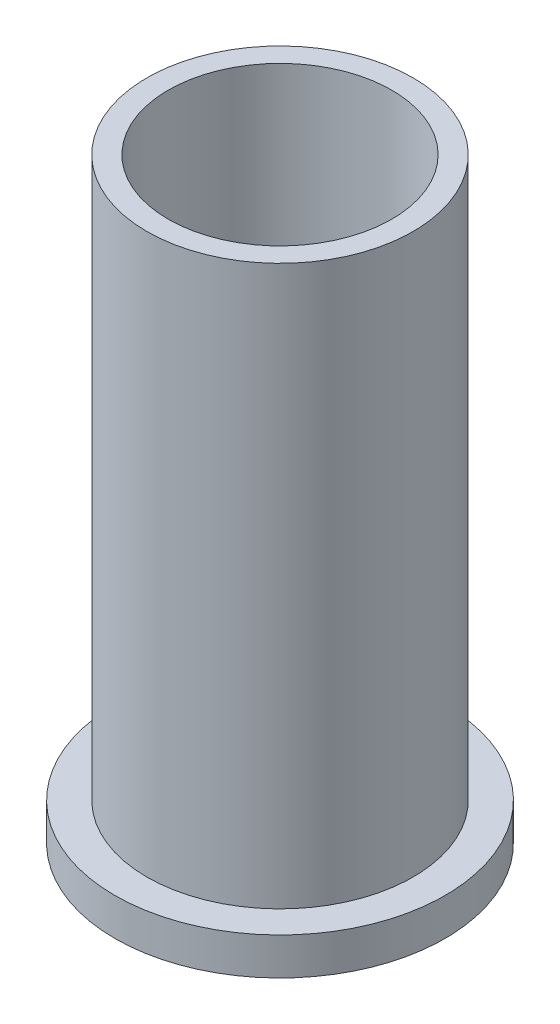
SolidWorks part; units mm, degrees
material "Delrin 2700 NC010, Low Viscosity Acetal Copolymer (SS)"
ref_plane "Front Plane" through (0, 0, 0) normal (0, 0, 1) x (1, 0, 0)
ref_plane "Top Plane" through (0, 0, 0) normal (0, 1, 0) x (1, 0, 0)
ref_plane "Right Plane" through (0, 0, 0) normal (1, 0, 0) x (0, 0, -1)
sketch "Sketch1" plane through (0, 0, 0) normal (0, 0, 1) x (1, 0, 0)
  line L0 (0, 0) -> (0, -32055.5422) construction
  line L1 (21, 0) -> (25, 0)
  line L2 (21, 0) -> (21, -112)
  line L4 (25, 0) -> (25, -105)
  line L10 (25, -105) -> (31, -105)
  line L12 (21, -112) -> (31, -112)
  line L13 (31, -105) -> (31, -112)
  point P2 (0, 0)
  point P6 (17.9511, -112.37)
  point P12 (0, 0)
  dimension "D1" = 25
  dimension "D2" = 112
  dimension "D3" = 21
  dimension "D4" = 7
  dimension "D5" = 31
revolve "Revolve1" add sketch "Sketch1" angle 360 about L0
